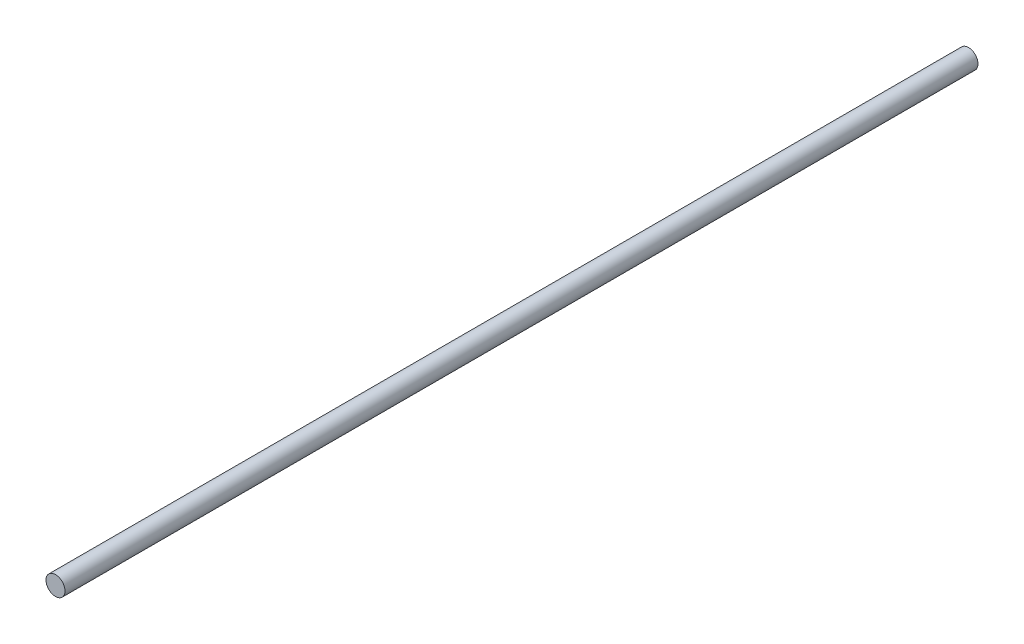
SolidWorks part; units mm, degrees
ref_plane "Front Plane" through (0, 0, 0) normal (0, 0, 1) x (1, 0, 0)
ref_plane "Top Plane" through (0, 0, 0) normal (0, 1, 0) x (1, 0, 0)
ref_plane "Right Plane" through (0, 0, 0) normal (1, 0, 0) x (0, 0, -1)
sketch "Sketch1" plane through (0, 0, 0) normal (0, 0, 1) x (1, 0, 0)
  circle A0 centre (0, 0) radius 1.5875
  dimension "D1" = 3.175
extrude "Boss-Extrude1" add sketch "Sketch1" along normal blind 152.4
